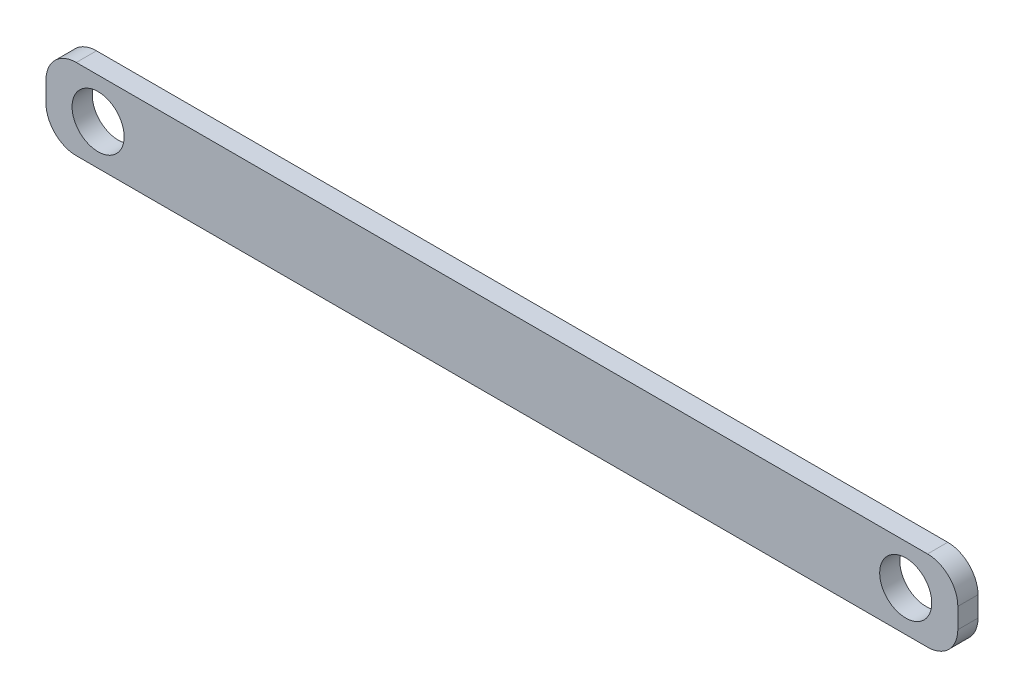
SolidWorks part; units mm, degrees
material "Teak"
ref_plane "Front Plane" through (0, 0, 0) normal (0, 0, 1) x (1, 0, 0)
ref_plane "Top Plane" through (0, 0, 0) normal (0, 1, 0) x (1, 0, 0)
ref_plane "Right Plane" through (0, 0, 0) normal (1, 0, 0) x (0, 0, -1)
sketch "Sketch1" plane through (0, 0, 0) normal (0, 0, 1) x (1, 0, 0)
  line L0 (-112.9, -10) -> (112.9, -10)
  line L1 (-112.9, -10) -> (-112.9, 10)
  line L2 (112.9, -10) -> (112.9, 10)
  line L3 (-112.9, 10) -> (112.9, 10)
  line L4 (-112.9, -10) -> (112.9, 10) construction
  line L5 (112.9, -10) -> (-112.9, 10) construction
  line L6 (-112.9, 0) -> (112.9, 0) construction
  line L7 (0, 10) -> (0, -10) construction
  circle A0 centre (-100, 0) radius 6.45
  circle A1 centre (100, 0) radius 6.45
  point P1 (0, 0)
  dimension "D3" = 12.9
  dimension "D1" = 200
  dimension "D2" = 20
  dimension "D4" = 12.9
extrude "Boss-Extrude1" add sketch "Sketch1" along normal blind 5
fillet "Fillet1" radius 7.5 4 edges at (-112.9, -10, 2.5) (-112.9, 10, 2.5) (112.9, -10, 2.5) (112.9, 10, 2.5)
equation "\"D1@Boss-Extrude1\"=5mm"
equation "\"p\"= 20mm"
equation "\"m\"= 1"
equation "\"hole_diam\"= 4mm"
equation "\"len_grip_1\" = 50mm"
equation "\"len_grip_2\" = 50mm"
equation "\"thick\" = 3.1mm"
equation "\"thick2\" = 20mm"
equation "\"wrist_cont_bearing_diam\"=3in"
equation "\"wrist_cont_bearing_thick\"=5/16in"
equation "\"len_forearm\" = 300mm"
equation "\"wrist_bearing_diam\"=3in"
equation "\"len_link\" = 7cm"
equation "\"D4@Sketch1\"=\"D3@Sketch1\""
